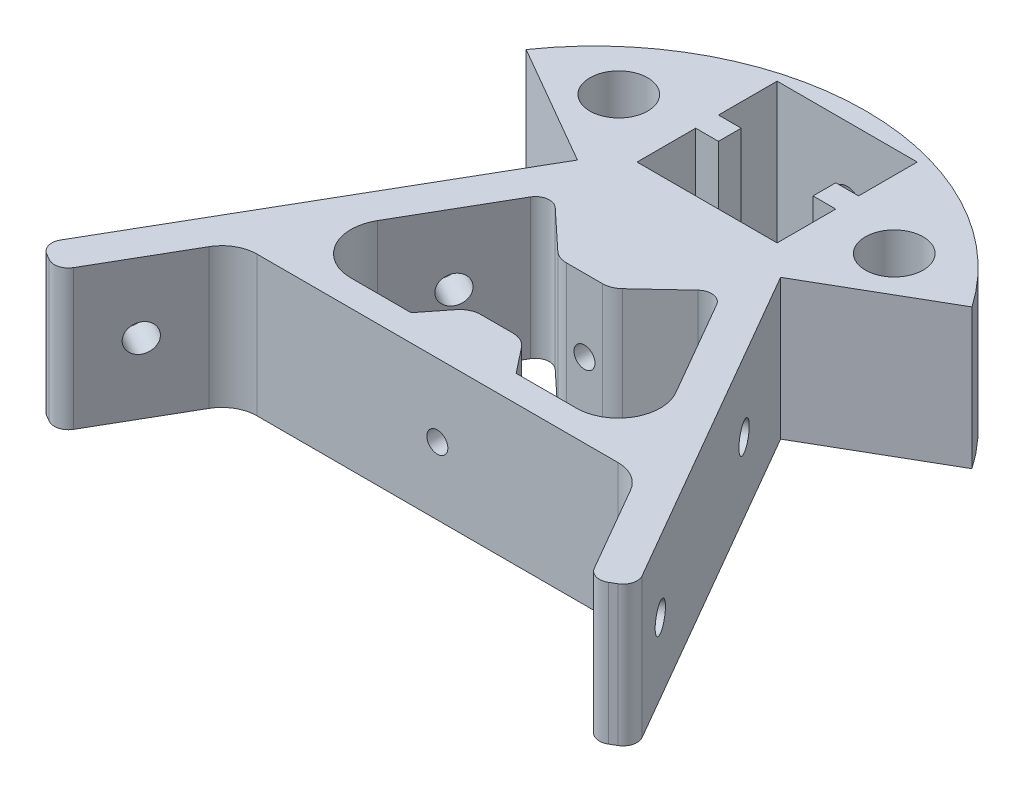
SolidWorks part; units mm, degrees
ref_plane "Front Plane" through (0, 0, 0) normal (0, 0, 1) x (1, 0, 0)
ref_plane "Top Plane" through (0, 0, 0) normal (0, 1, 0) x (1, 0, 0)
ref_plane "Right Plane" through (0, 0, 0) normal (1, 0, 0) x (0, 0, -1)
sketch "Sketch1" plane through (0, 0, 0) normal (0, 1, 0) x (1, 0, 0)
  line L0 (-28.6436, -10.5374) -> (-38.1699, -27.0374)
  line L1 (42.5, -24.5374) -> (14.5, 23.96)
  line L2 (-14.5, 23.96) -> (-42.5, -24.5374)
  line L3 (-42.5, -24.5374) -> (42.5, -24.5374) construction
  line L4 (-38.1699, -27.0374) -> (-42.5, -24.5374)
  line L5 (-28.6436, -10.5374) -> (28.6436, -10.5374)
  line L6 (28.6436, -10.5374) -> (38.1699, -27.0374)
  line L7 (38.1699, -27.0374) -> (42.5, -24.5374)
  line L8 (14.5, 23.96) -> (31.8205, 33.96)
  line L9 (-14.5, 23.96) -> (-31.8205, 33.96)
  line L10 (-12.0448, 18.2126) -> (-26.4785, -6.7874)
  line L11 (-26.4785, -6.7874) -> (-7.5, -6.7874)
  line L12 (26.4785, -6.7874) -> (12.0448, 18.2126)
  line L13 (-12.0448, 18.2126) -> (-3.75, 10.4626)
  line L14 (-7.5, -6.7874) -> (-3.75, -2.0374)
  line L15 (-3.75, -2.0374) -> (3.75, -2.0374)
  line L16 (3.75, -2.0374) -> (7.5, -6.7874)
  line L17 (7.5, -6.7874) -> (26.4785, -6.7874)
  line L18 (-3.75, 10.4626) -> (3.75, 10.4626)
  line L19 (3.75, 10.4626) -> (12.0448, 18.2126)
  line L20 (19.6603, 35.0222) -> (23.1603, 28.96) construction
  line L21 (-9.9995, 47.9626) -> (10.0005, 47.9626)
  line L22 (-9.9995, 47.9626) -> (-9.9995, 39.5876)
  line L23 (-9.9995, 27.9626) -> (10.0005, 27.9626)
  line L24 (10.0005, 47.9626) -> (10.0005, 39.5876)
  line L25 (31.8205, 33.96) -> (27.4913, 41.4584) construction
  line L26 (-9.9995, 36.3376) -> (-9.9995, 27.9626)
  line L27 (-9.9995, 39.5876) -> (-6.7495, 39.5876)
  line L28 (10.0005, 36.3376) -> (10.0005, 27.9626)
  line L29 (-9.9995, 36.3376) -> (-6.7495, 36.3376)
  line L30 (-6.7495, 39.5876) -> (-6.7495, 36.3376)
  line L31 (10.0005, 39.5876) -> (6.7505, 39.5876)
  line L33 (10.0005, 36.3376) -> (6.7505, 36.3376)
  line L34 (6.7505, 39.5876) -> (6.7505, 36.3376)
  circle A0 centre (0, 0) radius 24.5374 construction
  arc A1 (-31.8205, 33.96) -> (31.8205, 33.96) centre (0, 11.9054) cw
  circle A2 centre (19.6603, 35.0222) radius 4.125
  circle A3 centre (-19.6603, 35.0222) radius 4.125
  dimension "D7" = 38.7163
  dimension "D5" = 8.25
  dimension "D21" = 7
  dimension "D23" = 7
  dimension "D25" = 9.6597
  dimension "D1" = 85
  dimension "D2" = 5
  dimension "D3" = 5
  dimension "D4" = 14
  dimension "D6" = 56
  dimension "D8" = 20
  dimension "D9" = 20
  dimension "D10" = 5
  dimension "D11" = 3.75
  dimension "D12" = 15
  dimension "D13" = 5
  dimension "D14" = 8.5
  dimension "D15" = 7.5
  dimension "D16" = 25
  dimension "D17" = 12.5
  dimension "D18" = 36.0572
  dimension "D19" = 20
  dimension "D20" = 8.375
  dimension "D22" = 10
  dimension "D24" = 3.25
extrude "Boss-Extrude1" add sketch "Sketch1" along normal blind 20
fillet "Fillet2" radius 5 1 edges at (-28.6436, 10, 10.5374)
fillet "Fillet3" radius 5 1 edges at (28.6436, 10, 10.5374)
fillet "Fillet4" radius 6 1 edges at (-26.4785, 10, 6.7874)
fillet "Fillet5" radius 6 1 edges at (26.4785, 10, 6.7874)
fillet "Fillet6" radius 2 2 edges at (12.0448, 10, -18.2126) (-12.0448, 10, -18.2126)
fillet "Fillet7" radius 3 4 edges at (-3.75, 10, 2.0374) (3.75, 10, 2.0374) (3.75, 10, -10.4626) (-3.75, 10, -10.4626)
fillet "Fillet10" radius 2 4 edges at (42.5, 10, 24.5374) (38.1699, 10, 27.0374) (-38.1699, 10, 27.0374) (-42.5, 10, 24.5374)
hole_wizard "Upper Vertex Holes" positions "Sketch4" profile "Sketch5" hole size "#8" standard "ANSI Inch"
sketch "Sketch4" plane through (0, 0, 10.5374) normal (0, 0, 1) x (1, 0, 0)
  point P0 (0, 9.6326)
sketch "Sketch5" plane through (0, 9.6326, 10.5374) normal (1, 0, 0) x (0, -1, 0)
  line L0 (0, 0) -> (0, 30.9013)
  line L1 (0, 30.9013) -> (1.5, 30)
  line L2 (1.5, 30) -> (1.5, 0)
  line L5 (1.5, 0) -> (0, 0)
  line L10 (0, 30.9013) -> (-1.5, 30) construction
  line L11 (0, -6.35) -> (0, 107.95) construction
  dimension "Hole Dia." = 3
  dimension "Hole Depth" = 30
  dimension "Drill Angle" = 118
hole_wizard "#8 (0.199) Diameter Hole2" positions "Sketch7" profile "Sketch6" hole size "#8" standard "ANSI Inch" end condition through all
sketch "Sketch7" plane through (16.9199, 0, -9.7687) normal (-0.866, 0, 0.5) x (0.5, 0, 0.866)
  point P0 (33.4171, 10)
sketch "Sketch6" plane through (33.6284, 10, 19.1714) normal (0, 1, 0) x (0.5, 0, 0.866)
  line L0 (0, 0) -> (0, 41.9456)
  line L1 (0, 41.9456) -> (2, 41.9456)
  line L2 (2, 41.9456) -> (2, 0)
  line L5 (2, 0) -> (0, 0)
  line L11 (0, -6.35) -> (0, 107.95) construction
  dimension "Thru Hole Dia." = 4
  dimension "Thru Hole Depth" = 41.9456
hole_wizard "#8 (0.199) Diameter Hole3" positions "Sketch9" profile "Sketch8" hole size "#8" standard "ANSI Inch" end condition through all
sketch "Sketch9" plane through (-16.9199, 0, -9.7687) normal (0.866, 0, 0.5) x (0.5, 0, -0.866)
  point P0 (-33.4171, 10)
sketch "Sketch8" plane through (-33.6284, 10, 19.1714) normal (0, 1, 0) x (0.5, 0, -0.866)
  line L0 (0, 0) -> (0, 41.9456)
  line L1 (0, 41.9456) -> (2, 41.9456)
  line L2 (2, 41.9456) -> (2, 0)
  line L5 (2, 0) -> (0, 0)
  line L11 (0, -6.35) -> (0, 107.95) construction
  dimension "Thru Hole Dia." = 4
  dimension "Thru Hole Depth" = 41.9456
hole_wizard "#8 (0.199) Diameter Hole5" positions "Sketch13" profile "Sketch12" hole size "#8" standard "ANSI Inch"
sketch "Sketch13" plane through (16.9199, 0, -9.7687) normal (-0.866, 0, 0.5) x (0.5, 0, 0.866)
  point P0 (0.7458, 10)
sketch "Sketch12" plane through (17.2928, 10, -9.1228) normal (0, 1, 0) x (0.5, 0, 0.866)
  line L0 (0, 0) -> (0, 41.9456)
  line L1 (0, 41.9456) -> (2, 41.9456)
  line L2 (2, 41.9456) -> (2, 0)
  line L5 (2, 0) -> (0, 0)
  line L11 (0, -6.35) -> (0, 107.95) construction
  dimension "Thru Hole Dia." = 4
  dimension "Thru Hole Depth" = 41.9456
hole_wizard "#8 (0.199) Diameter Hole6" positions "Sketch17" profile "Sketch16" hole size "#8" standard "ANSI Inch"
sketch "Sketch17" plane through (-16.9199, 0, -9.7687) normal (0.866, 0, 0.5) x (0.5, 0, -0.866)
  point P0 (-0.7458, 10)
sketch "Sketch16" plane through (-17.2928, 10, -9.1228) normal (0, 1, 0) x (0.5, 0, -0.866)
  line L0 (0, 0) -> (0, 41.9456)
  line L1 (0, 41.9456) -> (2, 41.9456)
  line L2 (2, 41.9456) -> (2, 0)
  line L5 (2, 0) -> (0, 0)
  line L11 (0, -6.35) -> (0, 107.95) construction
  dimension "Thru Hole Dia." = 4
  dimension "Thru Hole Depth" = 41.9456
hole_wizard "#8 (0.199) Diameter Hole7" positions "Sketch19" profile "Sketch18" hole size "#8" standard "ANSI Inch"
sketch "Sketch19" plane through (0, 0, -47.9626) normal (0, 0, 1) x (1, 0, 0)
  point P0 (0.0005, 10)
sketch "Sketch18" plane through (0.0005, 10, -47.9626) normal (1, 0, 0) x (0, -1, 0)
  line L0 (0, 0) -> (0, 31.2017)
  line L1 (0, 31.2017) -> (2, 30)
  line L2 (2, 30) -> (2, 0)
  line L5 (2, 0) -> (0, 0)
  line L10 (0, 31.2017) -> (-2, 30) construction
  line L11 (0, -6.35) -> (0, 107.95) construction
  dimension "Hole Dia." = 4
  dimension "Hole Depth" = 30
  dimension "Drill Angle" = 118
sketch "Sketch21" [suppressed] plane through (0, 0, 10.5374) normal (0, 0, 1) x (1, 0, 0)
  line L0 (-25.7568, 20) -> (25.7568, 20) construction
  line L3 (-25.7568, 20) -> (-25.7568, 0) construction
  circle A0 centre (-15.5, 14.75) radius 1.5 construction
  circle A1 centre (15.5, 14.75) radius 1.5 construction
  dimension "D1" = 31
  dimension "D3" = 10.2569
  dimension "D4" = 3
  dimension "D2" = 5.25
hole_wizard "#8 (0.199) Diameter Hole8" [suppressed] positions "Sketch23" profile "Sketch22" hole size "#8" standard "ANSI Inch"
sketch "Sketch23" [suppressed] plane through (0, 0, 10.5374) normal (0, 0, 1) x (1, 0, 0)
  point P0 (-15.5, 14.75)
  point P3 (15.5, 14.75)
sketch "Sketch22" plane through (-15.5, 14.75, 10.5374) normal (1, 0, 0) x (0, -1, 0)
  line L0 (0, 0) -> (0, 4.9013)
  line L1 (0, 4.9013) -> (1.5, 4)
  line L2 (1.5, 4) -> (1.5, 0)
  line L5 (1.5, 0) -> (0, 0)
  line L10 (0, 4.9013) -> (-1.5, 4) construction
  line L11 (0, -6.35) -> (0, 107.95) construction
  dimension "Hole Dia." = 3
  dimension "Hole Depth" = 4
  dimension "Drill Angle" = 118
